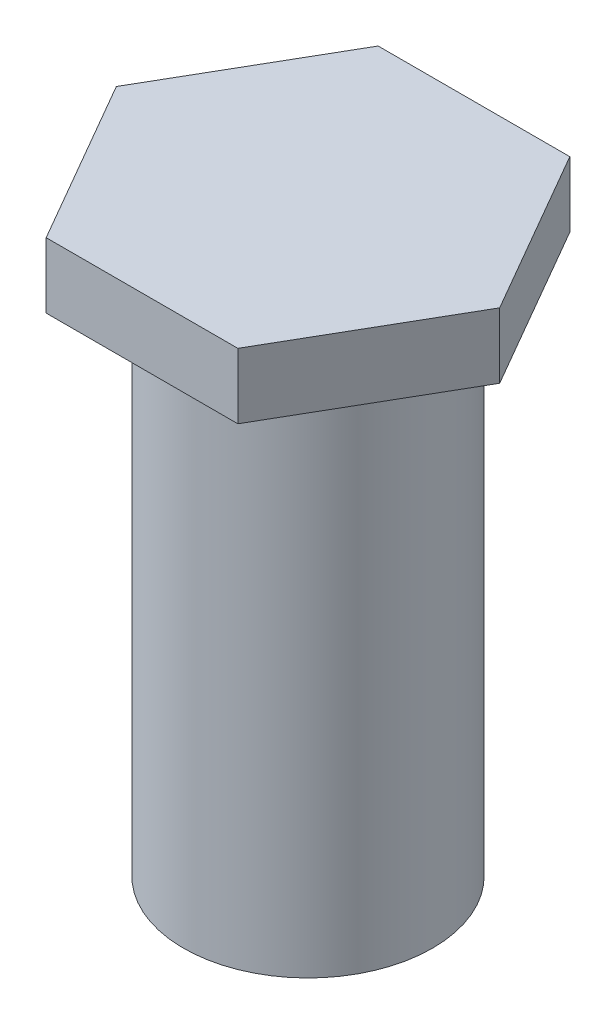
SolidWorks part; units mm, degrees
ref_plane "Alzado" through (0, 0, 0) normal (0, 0, 1) x (1, 0, 0)
ref_plane "Planta" through (0, 0, 0) normal (0, 1, 0) x (1, 0, 0)
ref_plane "Vista lateral" through (0, 0, 0) normal (1, 0, 0) x (0, 0, -1)
sketch "Croquis1" plane through (0, 0, 0) normal (0, 0, 1) x (1, 0, 0)
  line L0 (0, 0) -> (0, 20) construction
  line L1 (0, 0) -> (4.765, 0)
  line L2 (4.765, 0) -> (4.765, 20)
  line L3 (4.765, 20) -> (0, 20)
  line L4 (0, 0) -> (0, 20)
  dimension "D1" = 4.765
  dimension "D2" = 20
revolve "Revolución1" add sketch "Croquis1" angle 360 about L0
sketch "Croquis2" plane through (0, 20, 0) normal (0, 1, 0) x (1, 0, 0)
  line L1 (-7.3323, 0) -> (-3.6662, -6.35)
  line L2 (-3.6662, -6.35) -> (3.6662, -6.35)
  line L3 (3.6662, -6.35) -> (7.3323, 0)
  line L4 (7.3323, 0) -> (3.6662, 6.35)
  line L5 (3.6662, 6.35) -> (-3.6662, 6.35)
  line L6 (-3.6662, 6.35) -> (-7.3323, 0)
  circle A0 centre (0, 0) radius 6.35 construction
  dimension "D1" = 12.7
extrude "Saliente-Extruir1" add sketch "Croquis2" along normal blind 2.5
